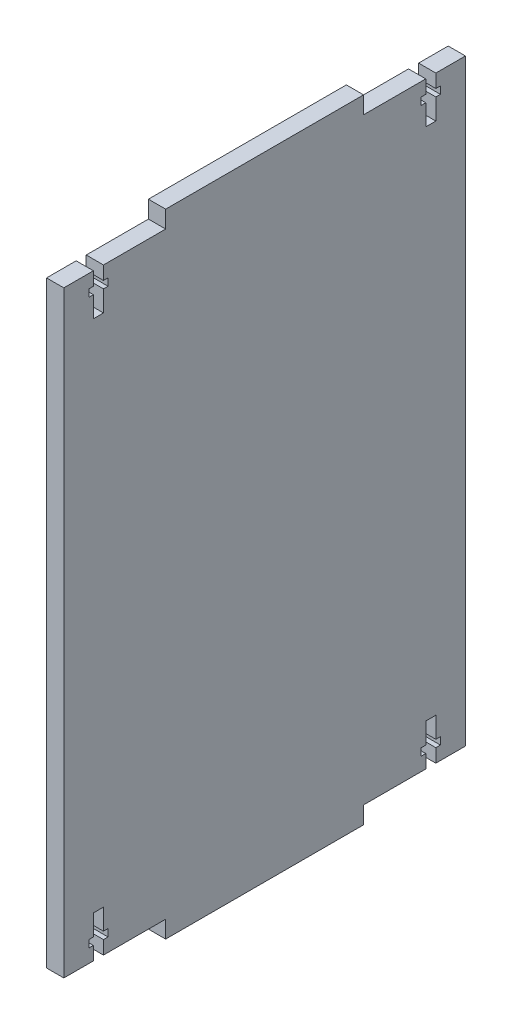
SolidWorks part; units mm, degrees
ref_plane "Front Plane" through (0, 0, 0) normal (0, 0, 1) x (1, 0, 0)
ref_plane "Top Plane" through (0, 0, 0) normal (0, 1, 0) x (1, 0, 0)
ref_plane "Right Plane" through (0, 0, 0) normal (1, 0, 0) x (0, 0, -1)
sketch "Sketch1" plane through (0, 0, 0) normal (1, 0, 0) x (0, 0, -1)
  line L1 (-35.6928, 37.9569) -> (83.7872, 37.9569)
  line L2 (-35.6928, 37.9569) -> (-35.6928, -139.8431)
  line L3 (-35.6928, -139.8431) -> (83.7872, -139.8431)
  line L4 (83.7872, 37.9569) -> (83.7872, -139.8431)
  dimension "D1" = 119.48
  dimension "D2" = 177.8
extrude "Boss-Extrude1" add sketch "Sketch1" along normal blind 5.13
sketch "Sketch2" plane through (5.13, 0, 0) normal (1, 0, 0) x (0, 0, -1)
  line L0 (-26.8928, 37.9569) -> (-23.8958, 37.9569)
  line L1 (83.7872, 37.9569) -> (-35.6928, 37.9569) construction
  line L2 (-23.8958, 37.9569) -> (-23.8958, 33.9619)
  line L3 (-23.8958, 33.9619) -> (-22.5368, 33.9619)
  line L4 (-22.5368, 33.9619) -> (-22.5368, 31.7949)
  line L5 (-22.5368, 31.7949) -> (-23.8958, 31.7949)
  line L6 (-23.8958, 31.7949) -> (-23.8958, 25.5879)
  line L7 (-23.8958, 25.5879) -> (-26.8928, 25.5879)
  line L8 (-26.8928, 25.5879) -> (-26.8928, 31.7949)
  line L9 (-26.8928, 31.7949) -> (-28.2518, 31.7949)
  line L10 (-28.2518, 31.7949) -> (-28.2518, 33.9619)
  line L11 (-28.2518, 33.9619) -> (-26.8928, 33.9619)
  line L12 (-26.8928, 33.9619) -> (-26.8928, 37.9569)
  line L13 (71.9872, 33.9619) -> (71.9872, 37.9569)
  line L14 (74.9842, 37.9569) -> (74.9842, 33.9619)
  line L15 (74.9842, 33.9619) -> (76.3432, 33.9619)
  line L16 (76.3432, 33.9619) -> (76.3432, 31.7949)
  line L17 (76.3432, 31.7949) -> (74.9842, 31.7949)
  line L18 (74.9842, 31.7949) -> (74.9842, 25.5879)
  line L19 (74.9842, 25.5879) -> (71.9872, 25.5879)
  line L20 (71.9872, 25.5879) -> (71.9872, 31.7949)
  line L21 (71.9872, 31.7949) -> (70.6282, 31.7949)
  line L22 (70.6282, 31.7949) -> (70.6282, 33.9619)
  line L23 (70.6282, 33.9619) -> (71.9872, 33.9619)
  line L24 (71.9872, 37.9569) -> (74.9842, 37.9569)
  line L25 (-35.6928, -50.9431) -> (83.7872, -50.9431) construction
  line L26 (-35.6928, 37.9569) -> (-35.6928, -139.8431) construction
  line L27 (83.7872, -139.8431) -> (83.7872, 37.9569) construction
  line L28 (76.3432, -133.6811) -> (74.9842, -133.6811)
  line L29 (76.3432, -135.8481) -> (76.3432, -133.6811)
  line L30 (74.9842, -135.8481) -> (76.3432, -135.8481)
  line L31 (74.9842, -139.8431) -> (74.9842, -135.8481)
  line L32 (71.9872, -139.8431) -> (74.9842, -139.8431)
  line L33 (71.9872, -135.8481) -> (71.9872, -139.8431)
  line L34 (70.6282, -135.8481) -> (71.9872, -135.8481)
  line L35 (70.6282, -133.6811) -> (70.6282, -135.8481)
  line L36 (71.9872, -133.6811) -> (70.6282, -133.6811)
  line L37 (71.9872, -127.4741) -> (71.9872, -133.6811)
  line L38 (74.9842, -127.4741) -> (71.9872, -127.4741)
  line L39 (74.9842, -133.6811) -> (74.9842, -127.4741)
  line L40 (-26.8928, -139.8431) -> (-23.8958, -139.8431)
  line L41 (-23.8958, -139.8431) -> (-23.8958, -135.8481)
  line L42 (-26.8928, -135.8481) -> (-26.8928, -139.8431)
  line L43 (-28.2518, -135.8481) -> (-26.8928, -135.8481)
  line L44 (-26.8928, -133.6811) -> (-28.2518, -133.6811)
  line L45 (-28.2518, -133.6811) -> (-28.2518, -135.8481)
  line L46 (-23.8958, -135.8481) -> (-22.5368, -135.8481)
  line L47 (-22.5368, -133.6811) -> (-23.8958, -133.6811)
  line L48 (-22.5368, -135.8481) -> (-22.5368, -133.6811)
  line L49 (-23.8958, -127.4741) -> (-26.8928, -127.4741)
  line L50 (-26.8928, -127.4741) -> (-26.8928, -133.6811)
  line L51 (-23.8958, -133.6811) -> (-23.8958, -127.4741)
  dimension "D1" = 2.167
  dimension "D2" = 2.997
  dimension "D3" = 2.997
  dimension "D4" = 3.995
  dimension "D5" = 3.995
  dimension "D6" = 1.359
  dimension "D7" = 1.359
  dimension "D8" = 6.207
  dimension "D9" = 6.207
  dimension "D10" = 1.359
  dimension "D12" = 8.8
  dimension "D11" = 2
extrude "Cut-Extrude1" cut sketch "Sketch2" against normal blind 5.13
sketch "Sketch5" plane through (0, 37.9569, 0) normal (0, 1, 0) x (1, 0, 0)
  line L0 (5.13, 53.4872) -> (0, 53.4872)
  line L1 (5.13, 53.4872) -> (5.13, -5.3928)
  line L2 (5.13, -5.3928) -> (0, -5.3928)
  line L3 (0, -5.3928) -> (0, 53.4872)
  line L4 (0, 71.9872) -> (0, -23.8958) construction
  line L5 (5.13, -35.6928) -> (0, -35.6928) construction
  line L6 (5.13, 71.9872) -> (5.13, -23.8958) construction
  point P6 (5.13, 24.0472)
  dimension "D1" = 59.74
extrude "Boss-Extrude2" add sketch "Sketch5" along normal blind 5.13
sketch "Sketch8" plane through (0, -139.8431, 0) normal (0, -1, 0) x (1, 0, 0)
  line L0 (5.13, 5.3928) -> (0, 5.3928)
  line L1 (5.13, 5.3928) -> (5.13, -53.4872)
  line L2 (5.13, -53.4872) -> (0, -53.4872)
  line L3 (0, -53.4872) -> (0, 5.3928)
  line L5 (5.13, 23.8958) -> (5.13, -71.9872) construction
  line L6 (0, 23.8958) -> (0, -71.9872) construction
  point P4 (0, -24.0472)
  dimension "D1" = 59.74
extrude "Boss-Extrude3" add sketch "Sketch8" along normal blind 5.13
equation "\"D1@Sketch5\" = \"D1@Sketch1\"/2"
equation "\"D1@Sketch8\" = \"D1@Sketch1\"/2"
